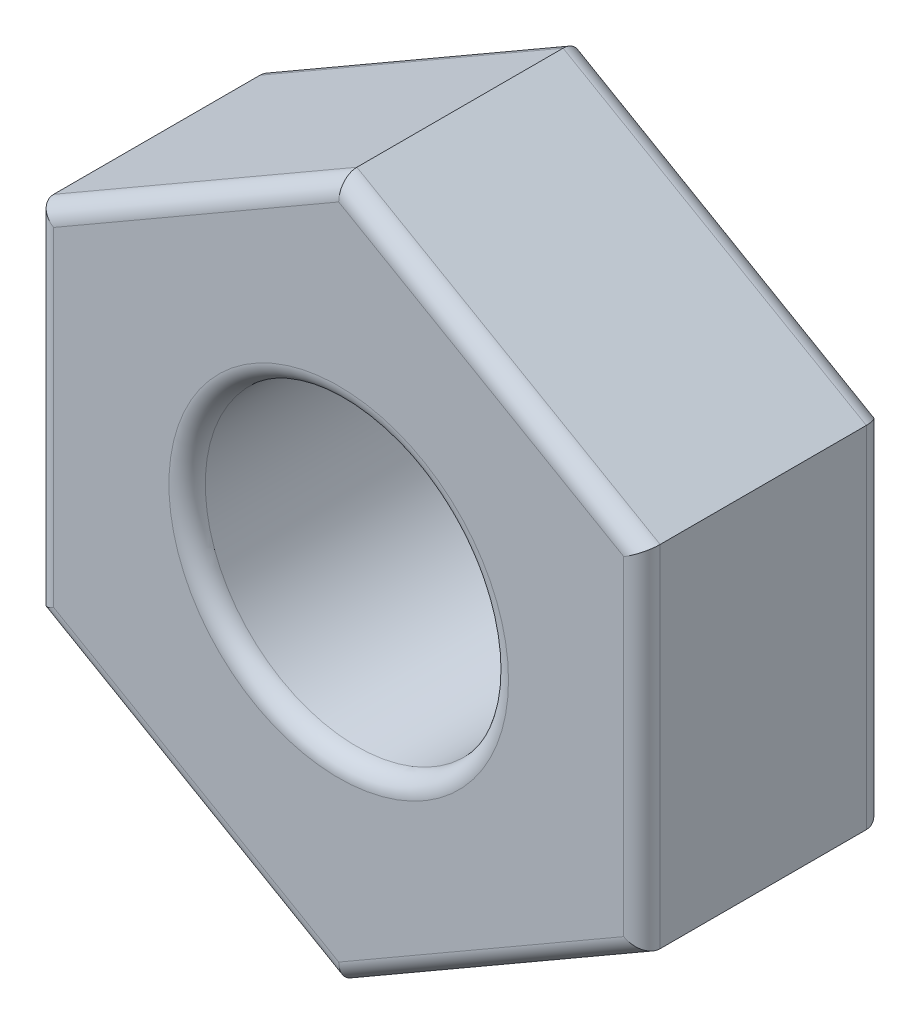
SolidWorks part; units mm, degrees
ref_plane "Front Plane" through (0, 0, 0) normal (0, 0, 1) x (1, 0, 0)
ref_plane "Top Plane" through (0, 0, 0) normal (0, 1, 0) x (1, 0, 0)
ref_plane "Right Plane" through (0, 0, 0) normal (1, 0, 0) x (0, 0, -1)
sketch "Sketch1" plane through (0, 0, 0) normal (0, 0, 1) x (1, 0, 0)
  line L1 (0, 2.8868) -> (-2.5, 1.4434)
  line L2 (-2.5, 1.4434) -> (-2.5, -1.4434)
  line L3 (-2.5, -1.4434) -> (0, -2.8868)
  line L4 (0, -2.8868) -> (2.5, -1.4434)
  line L5 (2.5, -1.4434) -> (2.5, 1.4434)
  line L6 (2.5, 1.4434) -> (0, 2.8868)
  circle A0 centre (0, 0) radius 2.5 construction
  circle A1 centre (0, 0) radius 1.25
  dimension "D1" = 2.5
  dimension "D2" = 5
extrude "Boss-Extrude1" add sketch "Sketch1" along normal blind 2
fillet "Fillet1" radius 0.15 14 edges at (1.25, 0, 0) (-1.25, 2.1651, 0) (-2.5, 0, 0) (-1.25, -2.1651, 0) (1.25, -2.1651, 0) (2.5, 0, 0) (1.25, 2.1651, 0) (1.25, 0, 2) (2.5, 0, 2) (1.25, -2.1651, 2) (-1.25, -2.1651, 2) (-2.5, 0, 2) (-1.25, 2.1651, 2) (1.25, 2.1651, 2)
